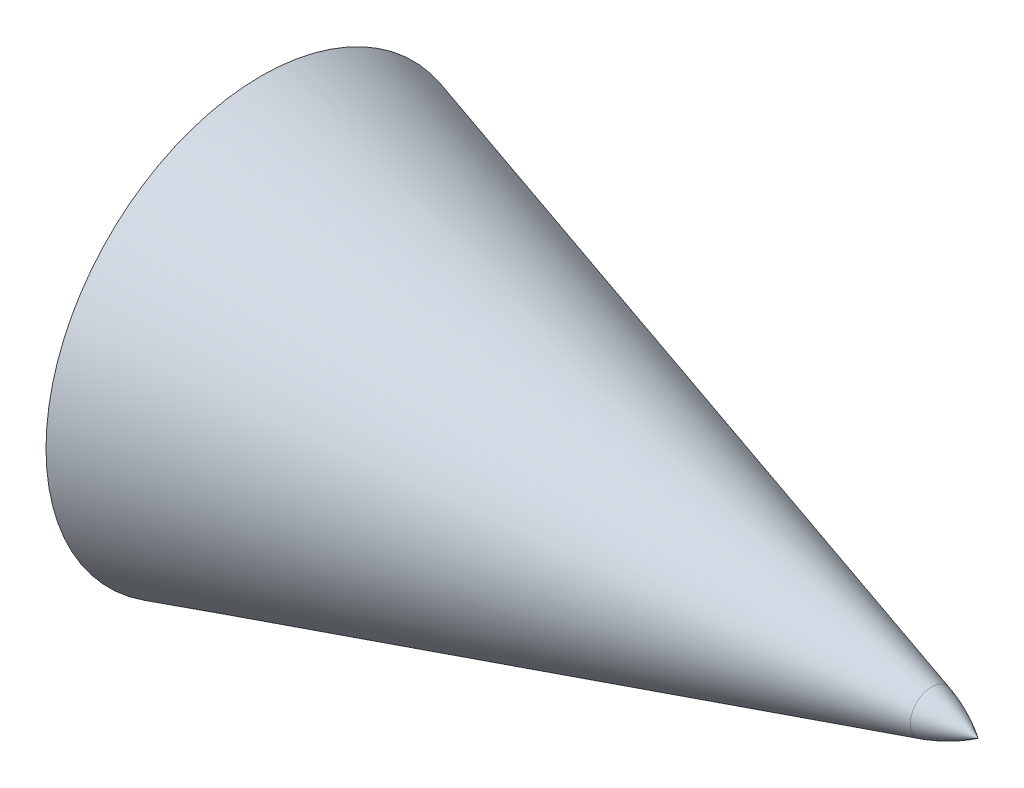
SolidWorks part; units mm, degrees
ref_plane "Front Plane" through (0, 0, 0) normal (0, 0, 1) x (1, 0, 0)
ref_plane "Top Plane" through (0, 0, 0) normal (0, 1, 0) x (1, 0, 0)
ref_plane "Right Plane" through (0, 0, 0) normal (1, 0, 0) x (0, 0, -1)
sketch "Sketch1" plane through (0, 0, 0) normal (0, 0, 1) x (1, 0, 0)
  line L0 (-90, 0) -> (90, 0) construction
  line L1 (-50, 15) -> (-3.238, 1.4845)
  line L2 (-50, 15) -> (-50, 0)
  line L3 (0, 0) -> (-50, 0)
  arc A0 (-3.238, 1.4845) -> (0, 0) centre (-6.5802, -10.0791) cw
  point P4 (0, 0)
  dimension "D1" = 15
  dimension "D2" = 50
revolve "Revolve3" add sketch "Sketch1" angle 360 about L0
sketch "Sketch3" plane through (0, 0, 0) normal (1, 0, 0) x (0, 0, -1)
  circle A0 centre (0, 0) radius 12.7
  dimension "D1" = 25.4
extrude "Cut-Extrude1" cut sketch "Sketch3" along normal blind 5 from offset 50
